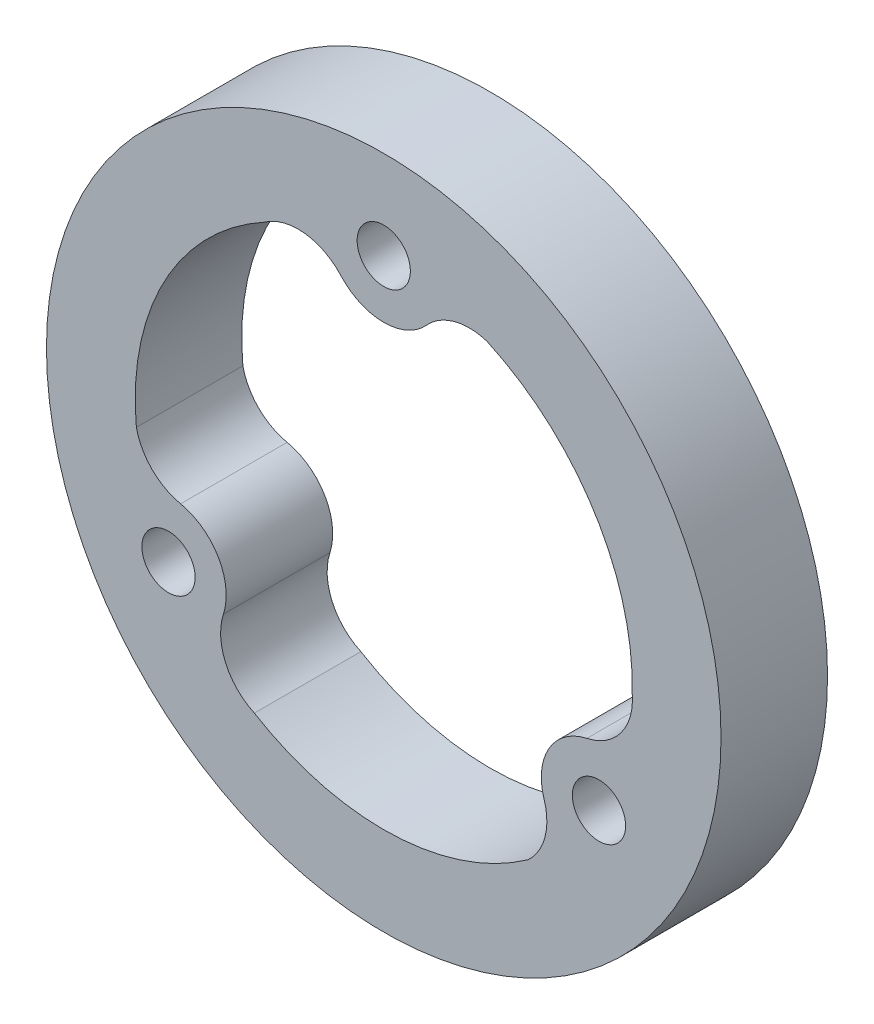
SolidWorks part; units mm, degrees
ref_plane "Plan de face" through (0, 0, 0) normal (0, 0, 1) x (1, 0, 0)
ref_plane "Plan de dessus" through (0, 0, 0) normal (0, 1, 0) x (1, 0, 0)
ref_plane "Plan de droite" through (0, 0, 0) normal (1, 0, 0) x (0, 0, -1)
sketch "Esquisse1" plane through (0, 0, 0) normal (0, 0, 1) x (1, 0, 0)
  line L0 (0, 14) -> (-12.125, -7.0011) construction
  line L1 (-12.125, -7.0011) -> (12.125, -7.0011) construction
  line L2 (12.125, -7.0011) -> (0, 14) construction
  circle A0 centre (0, 0) radius 19
  circle A2 centre (0, 14) radius 1.5
  arc A12 (-2.411, 11.8207) -> (2.411, 11.8207) centre (0, 14) ccw
  arc A16 (5.8094, 12.7378) -> (2.411, 11.8207) centre (4.8221, 9.6414) ccw
  arc A17 (-2.411, 11.8207) -> (-6.7074, 12.2887) centre (-4.8221, 9.6414) ccw
  arc A18 (-6.7074, 12.2887) -> (-13.9359, -1.3378) centre (0, 0) ccw
  arc A19 (8.1265, -11.4) -> (9.0315, -7.9984) centre (5.9386, -8.9967) ccw
  arc A20 (11.4425, -3.8223) -> (9.0315, -7.9984) centre (12.1244, -7) ccw
  arc A21 (11.4425, -3.8223) -> (13.996, -0.3356) centre (10.7607, -0.6447) ccw
  circle A22 centre (12.1244, -7) radius 1.5
  arc A23 (-13.9359, -1.3378) -> (-11.4425, -3.8223) centre (-10.7607, -0.6447) ccw
  arc A24 (-9.0315, -7.9984) -> (-11.4425, -3.8223) centre (-12.1244, -7) ccw
  arc A25 (-9.0315, -7.9984) -> (-7.2886, -11.9531) centre (-5.9386, -8.9967) ccw
  circle A26 centre (-12.1244, -7) radius 1.5
  arc A27 (-7.2886, -11.9531) -> (8.1265, -11.4) centre (0, 0) ccw
  arc A28 (13.996, -0.3356) -> (5.8094, 12.7378) centre (0, 0) ccw
  circle A29 centre (0, 14) radius 3.25 construction
  point P31 (0, 0)
  dimension "D1" = 38
  dimension "D2" = 3
  dimension "D3" = 3
  dimension "D4" = 6.5
  dimension "D5" = 14
  dimension "D8" = 14
  dimension "D9" = 3.25
  dimension "D10" = 14
  dimension "D11" = 3.25
  dimension "D12" = 24.25
  dimension "D13" = 24.25
  dimension "D6" = 60
  dimension "D7" = 60
  dimension "D14" = 10.78
  dimension "D15" = 10.78
extrude "Boss.-Extru.2" add sketch "Esquisse1" along normal blind 6
